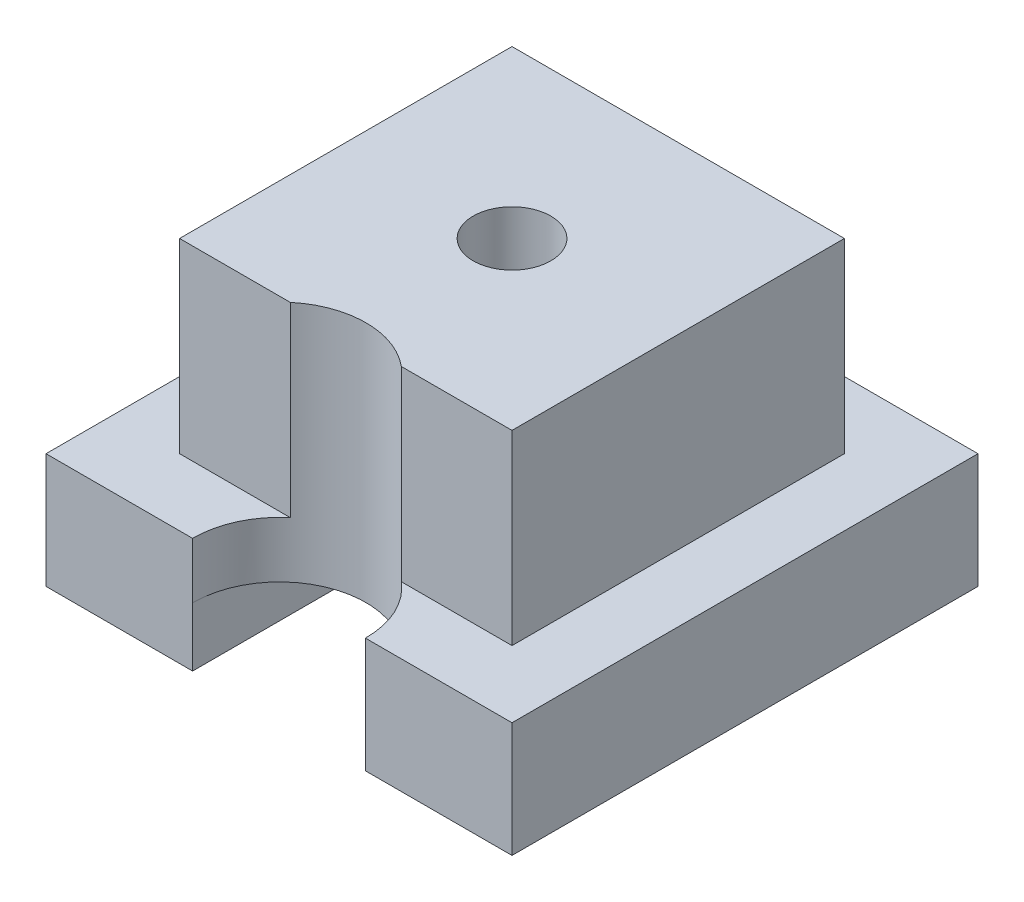
SolidWorks part; units mm, degrees
material "6061-T6 Al"
ref_plane "Front" through (0, 0, 0) normal (0, 0, 1) x (1, 0, 0)
ref_plane "Top" through (0, 0, 0) normal (0, 1, 0) x (1, 0, 0)
ref_plane "Right" through (0, 0, 0) normal (1, 0, 0) x (0, 0, -1)
sketch "Sketch1" plane through (0, 0, 0) normal (0, 1, 0) x (1, 0, 0)
  line L1 (-19.05, 19.05) -> (19.05, 19.05)
  line L2 (-19.05, 19.05) -> (-19.05, -19.05)
  line L3 (-19.05, -19.05) -> (19.05, -19.05)
  line L4 (19.05, 19.05) -> (19.05, -19.05)
  line L5 (-19.05, 19.05) -> (19.05, -19.05) construction
  line L6 (-19.05, -19.05) -> (19.05, 19.05) construction
  point P0 (0, 0)
  dimension "D1" = 38.1
extrude "Boss-Extrude1" add sketch "Sketch1" along normal blind 4.572
sketch "Sketch5" plane through (0, 0, 0) normal (0, 1, 0) x (1, 0, 0)
  line L1 (-13.589, 13.589) -> (13.589, 13.589)
  line L2 (-13.589, 13.589) -> (-13.589, -13.589)
  line L3 (-13.589, -13.589) -> (13.589, -13.589)
  line L4 (13.589, 13.589) -> (13.589, -13.589)
  line L5 (-13.589, 13.589) -> (13.589, -13.589) construction
  line L6 (-13.589, -13.589) -> (13.589, 13.589) construction
  point P0 (0, 0)
  dimension "D1" = 27.178
extrude "Boss-Extrude2" add sketch "Sketch5" along normal blind 19.812
sketch "Sketch2" plane through (0, 0, 0) normal (0, -1, 0) x (1, 0, 0)
  circle A0 centre (0, 19) radius 7.0635
  dimension "D1" = 14.127
  dimension "D2" = 19
extrude "Cut-Extrude1" cut sketch "Sketch2" against normal through all
hole_wizard "1/4-20 Tapped Hole1" positions "Sketch4" profile "Sketch3" tap size "1/4-20" standard "ANSI Inch" end condition through all
sketch "Sketch4" plane through (0, 0, 0) normal (0, -1, 0) x (-1, 0, 0)
  point P0 (0, 0)
sketch "Sketch3" plane through (0, 0, 0) normal (1, 0, 0) x (0, 0, -1)
  line L0 (0, 0) -> (0, 19.812)
  line L1 (0, 19.812) -> (3.175, 19.812)
  line L2 (3.175, 19.812) -> (3.175, 0)
  line L5 (3.175, 0) -> (0, 0)
  line L11 (0, -6.35) -> (0, 107.95) construction
  dimension "Thread Major Dia." = 6.35
  dimension "Thru Tap Drill Depth" = 19.812
sketch "Sketch6" plane through (0, 0, 0) normal (0, -1, 0) x (1, 0, 0)
  line L1 (19.05, -19.05) -> (7.0633, -19.05)
  line L2 (19.05, -19.05) -> (19.05, 19.05)
  line L3 (19.05, 19.05) -> (7.0633, 19.05)
  line L4 (7.0633, -19.05) -> (7.0633, 19.05)
  line L5 (-19.05, -19.05) -> (-7.0633, -19.05)
  line L6 (-19.05, -19.05) -> (-19.05, 19.05)
  line L7 (-19.05, 19.05) -> (-7.0633, 19.05)
  line L8 (-7.0633, -19.05) -> (-7.0633, 19.05)
extrude "Boss-Extrude3" add sketch "Sketch6" along normal blind 4.826
